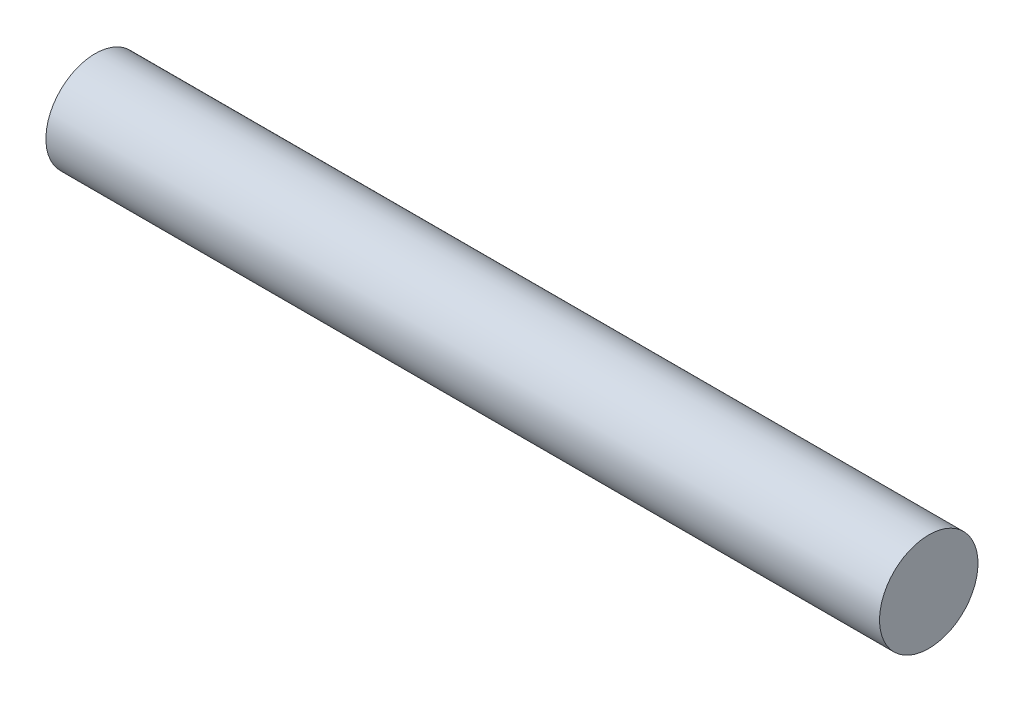
SolidWorks part; units mm, degrees
ref_plane "Front Plane" through (0, 0, 0) normal (0, 0, 1) x (1, 0, 0)
ref_plane "Top Plane" through (0, 0, 0) normal (0, 1, 0) x (1, 0, 0)
ref_plane "Right Plane" through (0, 0, 0) normal (1, 0, 0) x (0, 0, -1)
sketch "Sketch1" plane through (0, 0, 0) normal (1, 0, 0) x (0, 0, -1)
  circle A0 centre (0, 0) radius 0.15
  dimension "D1" = 0.3
extrude "Boss-Extrude1" add sketch "Sketch1" along normal blind 2.54 contours A0
